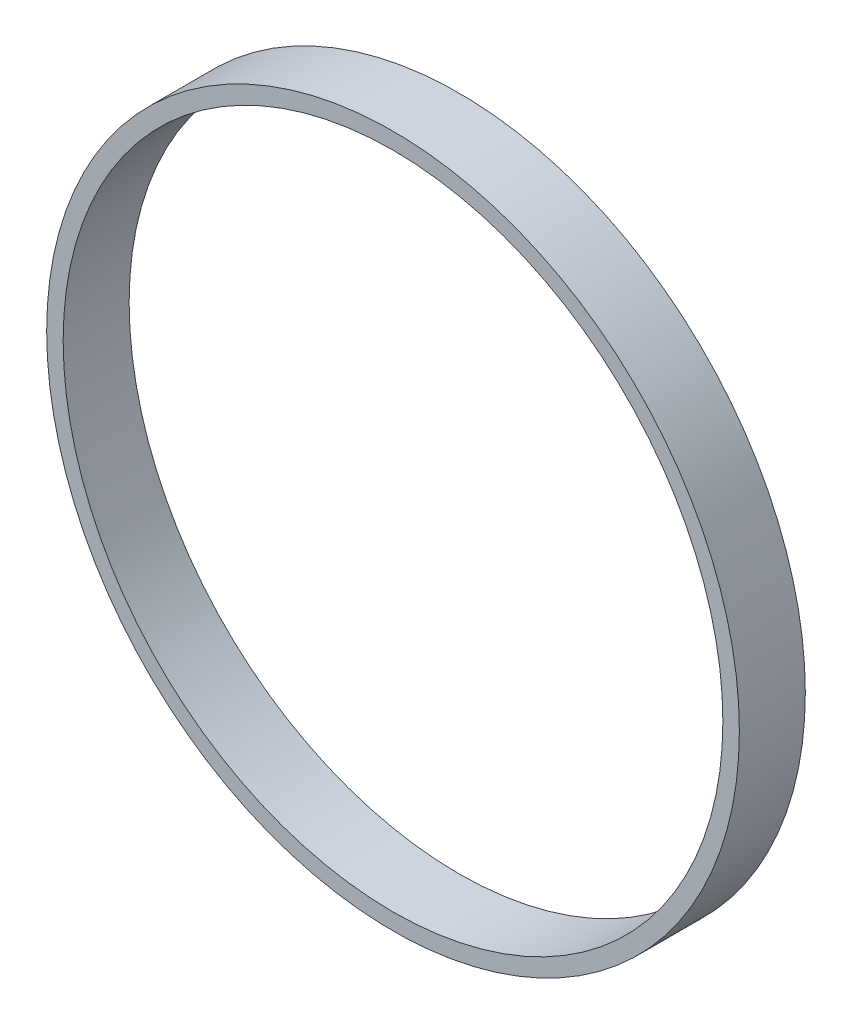
SolidWorks part; units mm, degrees
ref_plane "Front Plane" through (0, 0, 0) normal (0, 0, 1) x (1, 0, 0)
ref_plane "Top Plane" through (0, 0, 0) normal (0, 1, 0) x (1, 0, 0)
ref_plane "Right Plane" through (0, 0, 0) normal (1, 0, 0) x (0, 0, -1)
sketch "Sketch1" plane through (0, 0, 0) normal (0, 0, 1) x (1, 0, 0)
  circle A0 centre (0, 0) radius 100
  circle A1 centre (0, 0) radius 105
  dimension "D1" = 5
extrude "Boss-Extrude1" add sketch "Sketch1" along normal blind 20
sketch "Sketch3" plane through (0, 0, 0) normal (0, 1, 0) x (1, 0, 0)
  line L0 (0, 0) -> (0, 115.6873) construction
